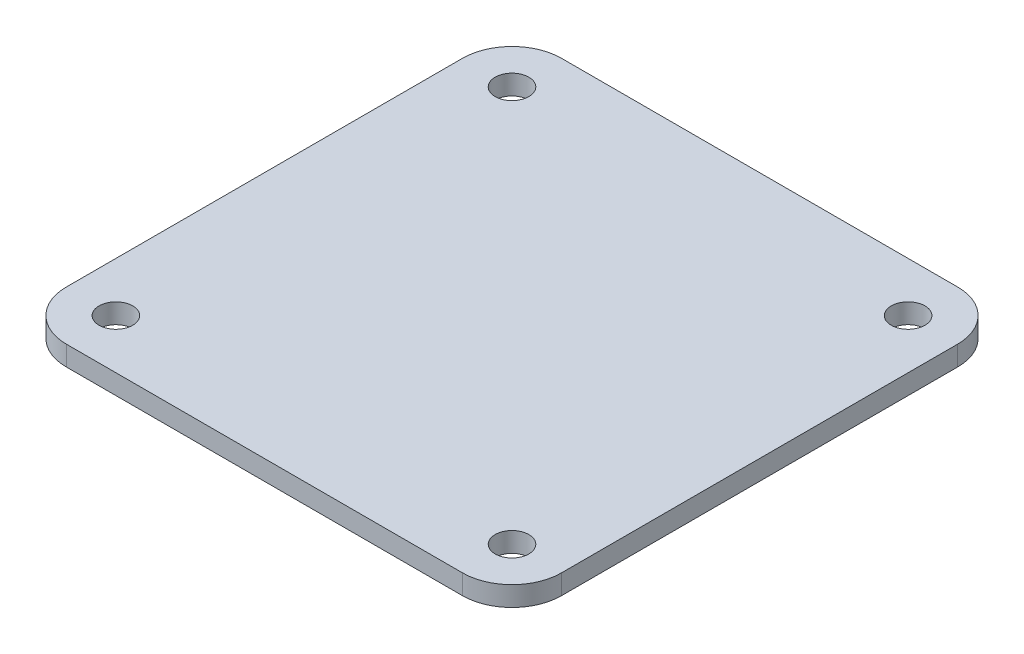
SolidWorks part; units mm, degrees
ref_plane "Front" through (0, 0, 0) normal (0, 0, 1) x (1, 0, 0)
ref_plane "Top" through (0, 0, 0) normal (0, 1, 0) x (1, 0, 0)
ref_plane "Right" through (0, 0, 0) normal (1, 0, 0) x (0, 0, -1)
sketch "Sketch1" plane through (0, -2, 0) normal (0, -1, 0) x (-1, 0, 0)
  line L0 (25, -20) -> (25, 20) construction
  line L1 (20, -25) -> (-20, -25) construction
  line L2 (-25, -20) -> (-25, 20) construction
  line L3 (20, 25) -> (-20, 25) construction
  line L4 (25, -20) -> (25, 20)
  line L5 (20, -25) -> (-20, -25)
  line L6 (-25, -20) -> (-25, 20)
  line L7 (20, 25) -> (-20, 25)
  arc A0 (25, 20) -> (20, 25) centre (20, 20) ccw construction
  arc A1 (20, -25) -> (25, -20) centre (20, -20) ccw construction
  arc A2 (-25, -20) -> (-20, -25) centre (-20, -20) ccw construction
  arc A3 (-20, 25) -> (-25, 20) centre (-20, 20) ccw construction
  arc A4 (25, 20) -> (20, 25) centre (20, 20) ccw
  arc A5 (20, -25) -> (25, -20) centre (20, -20) ccw
  arc A6 (-25, -20) -> (-20, -25) centre (-20, -20) ccw
  arc A7 (-20, 25) -> (-25, 20) centre (-20, 20) ccw
  circle A8 centre (20, -20) radius 1.7 construction
  circle A9 centre (-20, -20) radius 1.7 construction
  circle A10 centre (20, 20) radius 1.7 construction
  circle A11 centre (-20, 20) radius 1.7 construction
  circle A12 centre (20, -20) radius 1.7
  circle A13 centre (-20, -20) radius 1.7
  circle A14 centre (20, 20) radius 1.7
  circle A15 centre (-20, 20) radius 1.7
extrude "Boss-Extrude1" add sketch "Sketch1" along normal blind 2
